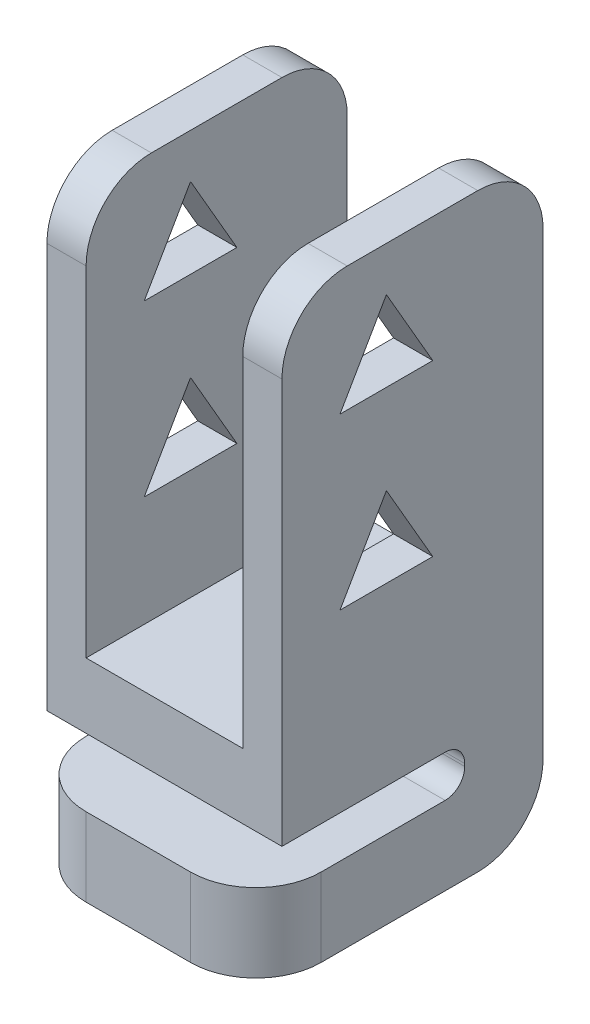
SolidWorks part; units mm, degrees
material "ABS"
ref_plane "Front Plane" through (0, 0, 0) normal (0, 0, 1) x (1, 0, 0)
ref_plane "Top Plane" through (0, 0, 0) normal (0, 1, 0) x (1, 0, 0)
ref_plane "Right Plane" through (0, 0, 0) normal (1, 0, 0) x (0, 0, -1)
sketch "Sketch2" plane through (0, 0, 0) normal (1, 0, 0) x (0, 0, -1)
  line L0 (2, -9) -> (2, -10.6)
  line L1 (-5, 9) -> (5, 9)
  line L2 (-5, 9) -> (-5, -9)
  line L3 (-5, -9) -> (2, -9)
  line L4 (5, 9) -> (5, -9)
  line L5 (-5, 9) -> (5, -9) construction
  line L6 (-5, -9) -> (5, 9) construction
  line L7 (2, -10.6) -> (-6, -10.6)
  line L8 (-6, -10.6) -> (-6, -13.6)
  line L9 (-6, -13.6) -> (5, -13.6)
  line L10 (5, -13.6) -> (5, -9)
  line L11 (2, -9) -> (5, -9) construction
  point P0 (0, 0)
  dimension "D1" = 1.6
  dimension "D2" = 18
  dimension "D3" = 10
  dimension "D4" = 3
  dimension "D5" = 11
  dimension "D6" = 3
extrude "Boss-Extrude1" add sketch "Sketch2" along normal mid plane 9
sketch "Sketch3" plane through (0, 0, 5) normal (0, 0, 1) x (1, 0, 0)
  line L0 (-4.5, 9) -> (-4.5, -9) construction
  line L1 (-3, 6.5) -> (3, 6.5) construction
  line L2 (-3, 6.5) -> (-3, -6.5)
  line L3 (-3, -6.5) -> (3, -6.5)
  line L4 (3, 6.5) -> (3, -6.5)
  line L5 (-3, 6.5) -> (3, -6.5) construction
  line L6 (-3, -6.5) -> (3, 6.5) construction
  line L7 (4.5, 9) -> (-4.5, 9) construction
  line L8 (-3, 6.5) -> (-3, 9)
  line L9 (-3, 9) -> (3, 9)
  line L10 (3, 9) -> (3, 6.5)
  point P0 (0, 0)
  point P7 (-4.5, 0)
  point P10 (0, 9)
  dimension "D1" = 6
  dimension "D2" = 13
extrude "Cut-Extrude1" cut sketch "Sketch3" against normal up to surface (10 mm away) up to face at (0, -2.3, -5)
sketch "Sketch4" plane through (0, 0, 0) normal (1, 0, 0) x (0, 0, -1)
  line L1 (0.7754, 4.225) -> (-1, 7.3)
  line L2 (-1, 7.3) -> (-2.7754, 4.225)
  line L3 (-2.7754, 4.225) -> (0.7754, 4.225)
  line L4 (0.7754, -2.275) -> (-1, 0.8)
  line L5 (-1, 0.8) -> (-2.7754, -2.275)
  line L6 (-2.7754, -2.275) -> (0.7754, -2.275)
  line L7 (5, -13.6) -> (5, 9) construction
  line L8 (5, -6.5) -> (-5, -6.5) construction
  circle A0 centre (-1, 5.25) radius 1.025 construction
  circle A1 centre (-1, -1.25) radius 1.025 construction
  circle A4 centre (-1, 5.25) radius 1.025 construction
  circle A5 centre (-1, -1.25) radius 1.025 construction
  dimension "D4" = 2.05
  dimension "D1" = 6
  dimension "D2" = 5.25
  dimension "D3" = 6.5
extrude "Cut-Extrude2" cut sketch "Sketch4" against normal through all and the other way through all
fillet "Fillet1" radius 2.5 7 edges at (0, -13.6, -5) (-3.75, 9, -5) (3.75, 9, -5) (-3.75, 9, 5) (3.75, 9, 5) (4.5, -12.1, 6) (-4.5, -12.1, 6)
fillet "Fillet2" radius 0.75 2 edges at (0, -10.6, -2) (0, -9, -2)
